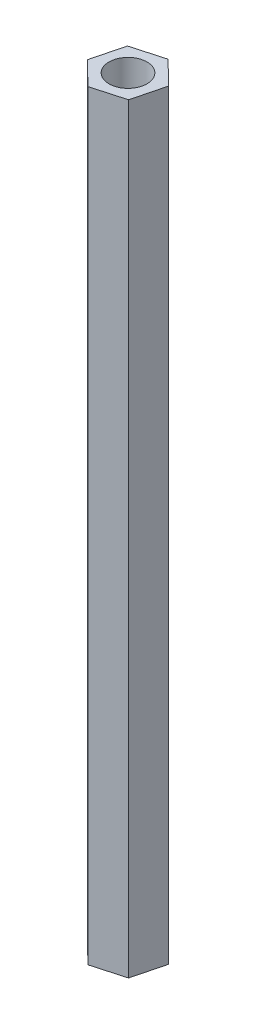
SolidWorks part; units mm, degrees
ref_plane "Front Plane" through (0, 0, 0) normal (0, 0, 1) x (1, 0, 0)
ref_plane "Top Plane" through (0, 0, 0) normal (0, 1, 0) x (1, 0, 0)
ref_plane "Right Plane" through (0, 0, 0) normal (1, 0, 0) x (0, 0, -1)
sketch "Sketch1" plane through (0, 0, 0) normal (0, 1, 0) x (1, 0, 0)
  line L1 (1.9306, -1.9018) -> (2.7878, 1.4546)
  line L2 (2.7878, 1.4546) -> (0.3097, 3.8751)
  line L3 (0.3097, 3.8751) -> (-3.0256, 2.9392)
  line L4 (-3.0256, 2.9392) -> (-3.8828, -0.4172)
  line L5 (-3.8828, -0.4172) -> (-1.4046, -2.8377)
  line L6 (-1.4046, -2.8377) -> (1.9306, -1.9018)
  circle A0 centre (-0.5475, 0.5187) radius 3 construction
  circle A1 centre (-0.5475, 0.5187) radius 2
  dimension "D1" = 6
extrude "Boss-Extrude1" add sketch "Sketch1" along normal blind 80
